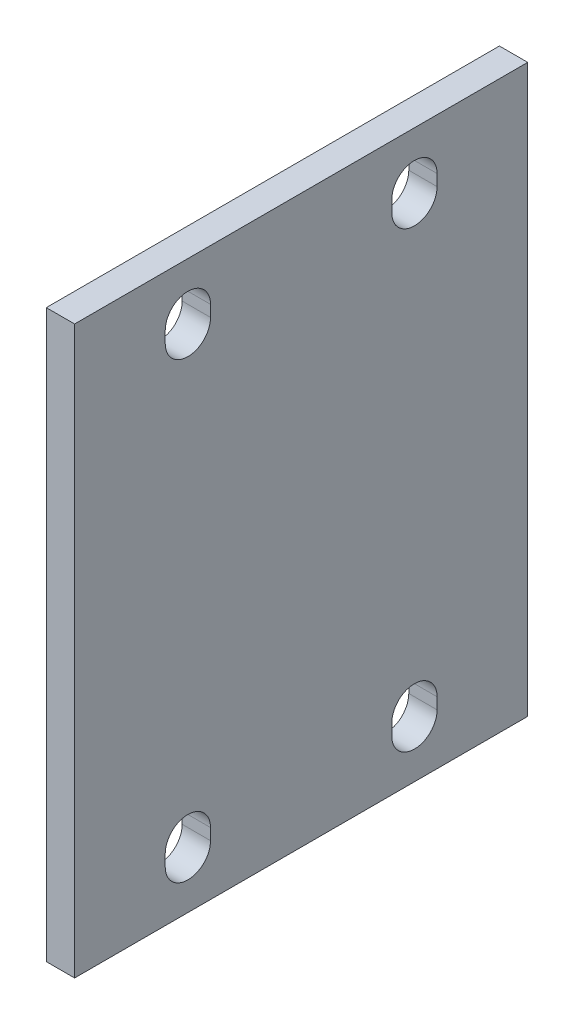
SolidWorks part; units mm, degrees
ref_plane "Front Plane" through (0, 0, 0) normal (0, 0, 1) x (1, 0, 0)
ref_plane "Top Plane" through (0, 0, 0) normal (0, 1, 0) x (1, 0, 0)
ref_plane "Right Plane" through (0, 0, 0) normal (1, 0, 0) x (0, 0, -1)
sketch "Sketch1" plane through (0, 0, 0) normal (1, 0, 0) x (0, 0, -1)
  line L0 (0, 0) -> (0, -75) construction
  line L1 (-40, 50) -> (40, 50)
  line L2 (-40, 50) -> (-40, -50)
  line L3 (-40, -50) -> (40, -50)
  line L4 (40, 50) -> (40, -50)
  line L5 (-40, 50) -> (40, -50) construction
  line L6 (-40, -50) -> (40, 50) construction
  line L7 (0, 0) -> (40, 0) construction
  line L8 (-40, 40) -> (40, 40) construction
  line L9 (-20, 41) -> (-20, 39) construction
  line L10 (-16, 41) -> (-16, 39)
  line L11 (-24, 41) -> (-24, 39)
  line L12 (20, 41) -> (20, 39) construction
  line L13 (16, 41) -> (16, 39)
  line L14 (24, 41) -> (24, 39)
  line L15 (-20, -41) -> (-20, -39) construction
  line L16 (-16, -41) -> (-16, -39)
  line L17 (-24, -41) -> (-24, -39)
  line L18 (20, -41) -> (20, -39) construction
  line L19 (16, -41) -> (16, -39)
  line L20 (24, -41) -> (24, -39)
  line L21 (-40, -50) -> (-18.4526, -86.0341)
  line L22 (40, -50) -> (18.4526, -86.0341)
  arc A0 (-16, 41) -> (-24, 41) centre (-20, 41) ccw
  arc A1 (-24, 39) -> (-16, 39) centre (-20, 39) ccw
  arc A2 (16, 41) -> (24, 41) centre (20, 41) cw
  arc A3 (24, 39) -> (16, 39) centre (20, 39) cw
  arc A4 (-16, -41) -> (-24, -41) centre (-20, -41) cw
  arc A5 (-24, -39) -> (-16, -39) centre (-20, -39) cw
  arc A6 (16, -41) -> (24, -41) centre (20, -41) ccw
  arc A7 (24, -39) -> (16, -39) centre (20, -39) ccw
  circle A8 centre (0, -75) radius 14
  circle A9 centre (0, -75) radius 17.5 construction
  circle A10 centre (17.5, -75) radius 2
  circle A11 centre (0, -92.5) radius 2
  circle A12 centre (-17.5, -75) radius 2
  circle A13 centre (0, -57.5) radius 2
  circle A14 centre (0, -75) radius 21.5
  point P0 (0, 0)
  point P14 (-20, 40)
  point P22 (20, 40)
  point P27 (-20, -40)
  point P34 (20, -40)
  point P51 (0, -75)
  dimension "D2" = 4
  dimension "D6" = 28
  dimension "D7" = 35
  dimension "D8" = 4
  dimension "D10" = 43
  dimension "D11" = 25
  dimension "D1" = 100
  dimension "D3" = 2
  dimension "D4" = 10
  dimension "D5" = 20
  dimension "D12" = 80
  dimension "D9" = 4
extrude "Boss-Extrude1" add sketch "Sketch1" along normal blind 5 contours L4 L1 L2 L3 A7 L20 A6 L19 A1 L11 A0 L10 L14 A3 L13 A2 L17 A5 L16 A4 | A14 L22 L3 L21 | A14 A8 A10 A11 A12 A13
sketch "Sketch3" plane through (5, 0, 0) normal (1, 0, 0) x (0, 0, -1)
  line L0 (-40, -50) -> (40, -50)
  line L1 (40, -50) -> (40, -105.1278)
  line L2 (40, -105.1278) -> (-40, -105.1278)
  line L3 (-40, -105.1278) -> (-40, -50)
extrude "Cut-Extrude1" cut sketch "Sketch3" against normal through all
